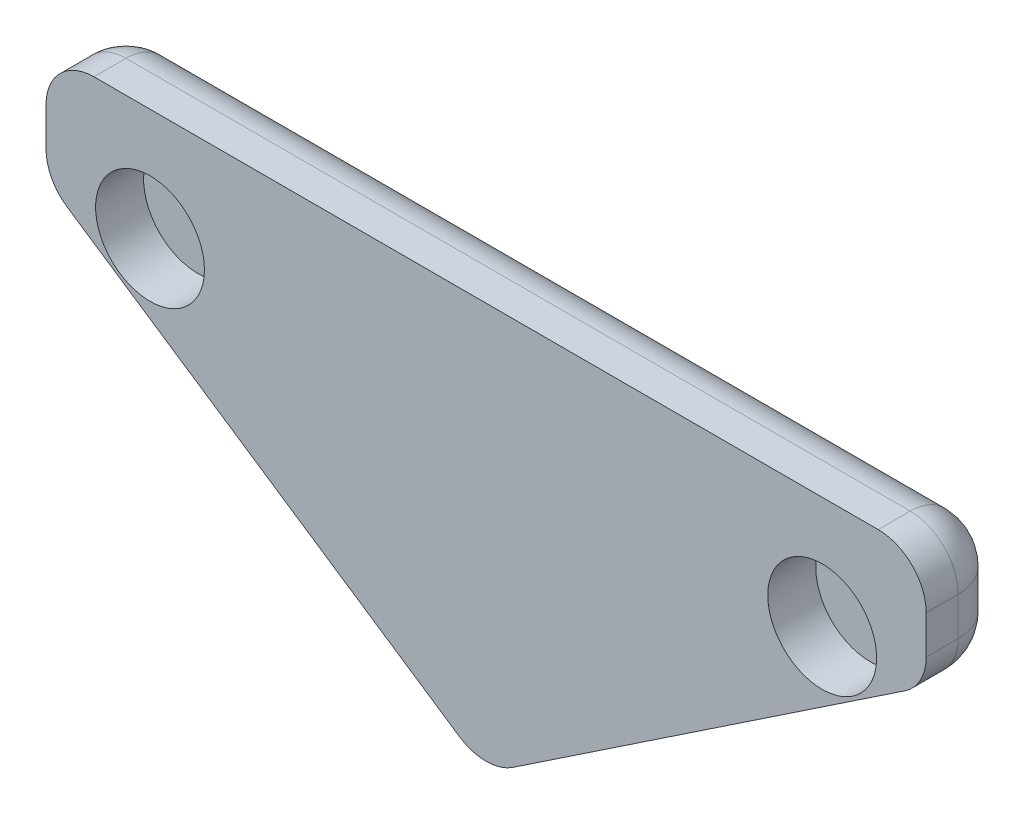
SolidWorks part; units mm, degrees
ref_plane "Front Plane" through (0, 0, 0) normal (0, 0, 1) x (1, 0, 0)
ref_plane "Top Plane" through (0, 0, 0) normal (0, 1, 0) x (1, 0, 0)
ref_plane "Right Plane" through (0, 0, 0) normal (1, 0, 0) x (0, 0, -1)
sketch "Sketch1" plane through (0, 0, 0) normal (0, 0, 1) x (1, 0, 0)
  line L0 (-7.5642, 12.7) -> (-7.5642, 9.2)
  line L3 (-7.5642, 9.2) -> (6.1858, 0)
  line L4 (6.1858, 0) -> (6.1858, 12.7)
  line L6 (6.1858, 12.7) -> (-7.5642, 12.7)
  line L7 (-4.3142, 12.7) -> (-4.3142, 5.95) construction
  line L8 (-7.5642, 9.2) -> (6.1858, 9.2) construction
  dimension "D1" = 3.5
  dimension "D2" = 3.25
  dimension "D3" = 13.75
extrude "Boss-Extrude1" add sketch "Sketch1" along normal blind 2.5
sketch "Sketch2" plane through (0, 0, 2.5) normal (0, 0, 1) x (1, 0, 0)
  line L0 (-7.5642, 9.2) -> (6.1858, 9.2) construction
  line L1 (-7.5642, 12.7) -> (-7.5642, 9.2) construction
  line L2 (6.1858, 0) -> (6.1858, 12.7) construction
  line L3 (-4.3142, 12.7) -> (-4.3142, 0) construction
  line L4 (6.1858, 12.7) -> (-7.5642, 12.7) construction
  circle A0 centre (-4.3142, 9.2) radius 1.7
  dimension "D1" = 3.5
  dimension "D2" = 3.25
extrude "Cut-Extrude1" cut sketch "Sketch2" against normal blind 1.5
mirror "Mirror2" about plane through (6.1858, 0, 2.5) normal (-1, 0, 0) of bodies 103
fillet "Fillet1" radius 1.5 10 edges at (-7.5642, 12.7, 1.25) (-7.5642, 10.95, 0) (6.1858, 12.7, 0) (19.9358, 12.7, 1.25) (19.9358, 9.2, 1.25) (19.9358, 10.95, 0) (13.0608, 4.6, 0) (6.1858, 0, 1.25) (-0.6892, 4.6, 0) (-7.5642, 9.2, 1.25)
